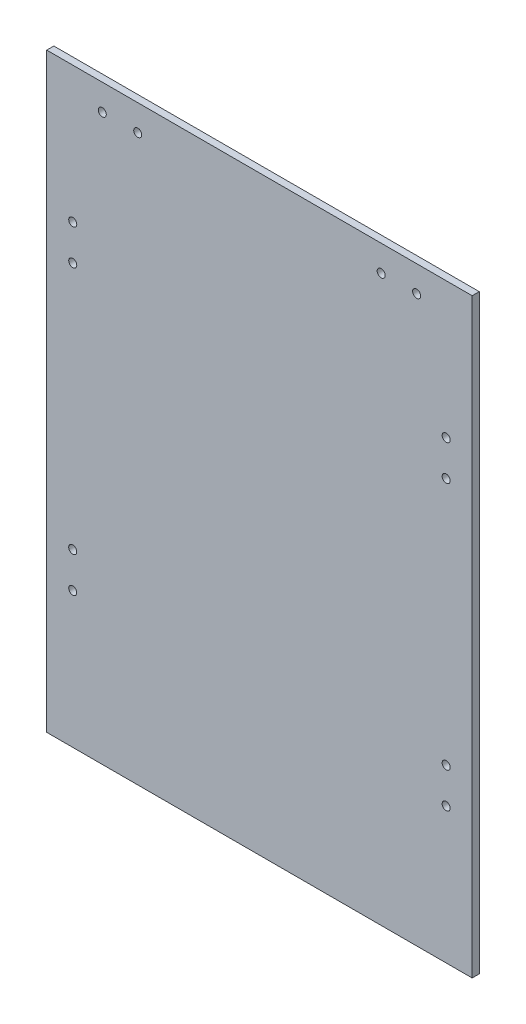
SolidWorks part; units mm, degrees
ref_plane "Plan de face" through (0, 0, 0) normal (0, 0, 1) x (1, 0, 0)
ref_plane "Plan de dessus" through (0, 0, 0) normal (0, 1, 0) x (1, 0, 0)
ref_plane "Plan de droite" through (0, 0, 0) normal (1, 0, 0) x (0, 0, -1)
sketch "Esquisse1" plane through (0, 0, 0) normal (0, 0, 1) x (1, 0, 0)
  line L1 (90, -125) -> (-90, -125)
  line L2 (90, -125) -> (90, 125)
  line L3 (90, 125) -> (-90, 125)
  line L4 (-90, -125) -> (-90, 125)
  line L5 (90, -125) -> (-90, 125) construction
  line L6 (90, 125) -> (-90, -125) construction
  point P0 (0, 0)
  dimension "D1" = 180
  dimension "D2" = 250
extrude "Boss.-Extru.1" add sketch "Esquisse1" along normal mid plane 3
sketch "Esquisse2" plane through (0, 0, 1.5) normal (0, 0, 1) x (1, 0, 0)
  line L0 (-66.5, 114) -> (-51.5, 114) construction
  line L1 (-59, 114) -> (-59, 125) construction
  line L2 (90, 125) -> (-90, 125) construction
  line L3 (0, 125) -> (0, -125) construction
  line L4 (-90, -125) -> (90, -125) construction
  circle A0 centre (-51.5, 114) radius 1.7
  circle A1 centre (-66.5, 114) radius 1.7
  circle A2 centre (51.5, 114) radius 1.7
  circle A3 centre (66.5, 114) radius 1.7
  point P12 (-64.2827, 125)
  dimension "D1" = 3.4
  dimension "D2" = 15
  dimension "D3" = 11
  dimension "D4" = 59
extrude "Enlèv. mat.-Extru.1" cut sketch "Esquisse2" against normal through all
sketch "Esquisse3" plane through (0, 0, 1.5) normal (0, 0, 1) x (1, 0, 0)
  line L0 (-79, 67.5) -> (-79, 52.5) construction
  line L1 (-79, 60) -> (-90, 60) construction
  line L2 (-90, 125) -> (-90, -125) construction
  line L3 (0, 0) -> (-90, 0) construction
  line L4 (0, 0) -> (0, 125) construction
  line L5 (90, 125) -> (-90, 125) construction
  circle A0 centre (-79, 67.5) radius 1.7
  circle A1 centre (-79, 52.5) radius 1.7
  circle A2 centre (-79, -52.5) radius 1.7
  circle A3 centre (-79, -67.5) radius 1.7
  circle A4 centre (79, -67.5) radius 1.7
  circle A5 centre (79, -52.5) radius 1.7
  circle A6 centre (79, 52.5) radius 1.7
  circle A7 centre (79, 67.5) radius 1.7
  dimension "D3" = 3.4
  dimension "D1" = 15
  dimension "D2" = 11
  dimension "D4" = 60
extrude "Enlèv. mat.-Extru.2" cut sketch "Esquisse3" against normal through all
